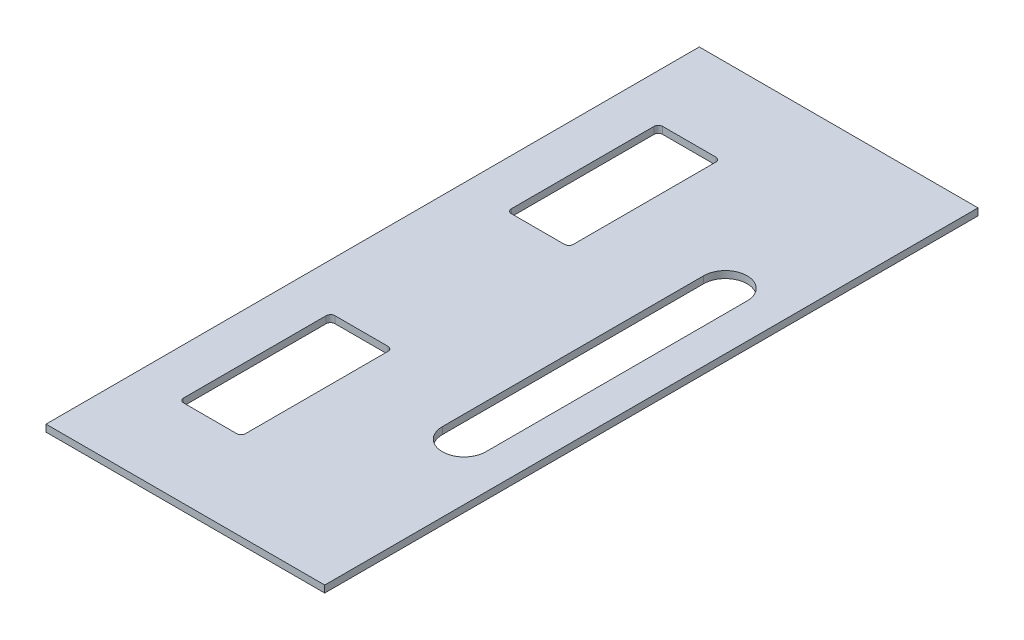
SolidWorks part; units mm, degrees
ref_plane "Front Plane" through (0, 0, 0) normal (0, 0, 1) x (1, 0, 0)
ref_plane "Top Plane" through (0, 0, 0) normal (0, 1, 0) x (1, 0, 0)
ref_plane "Right Plane" through (0, 0, 0) normal (1, 0, 0) x (0, 0, -1)
sketch "Sketch4" plane through (0, 0, 0) normal (0, 1, 0) x (1, 0, 0)
  line L0 (0, 0) -> (320, 0)
  line L2 (0, 750) -> (320, 750)
  line L3 (0, 750) -> (0, 0)
  line L4 (0, 0) -> (320, 0)
  line L5 (320, 750) -> (320, 0)
  dimension "D1" = 320
  dimension "D2" = 750
extrude "Boss-Extrude3" add sketch "Sketch4" along normal blind 8 contours L5 L2 L3 L0
sketch "Sketch8" plane through (0, 8, 0) normal (0, 1, 0) x (1, 0, 0)
  line L0 (-4.4, 0) -> (4.4, 0) construction
  line L1 (119, 100) -> (58, 100)
  line L2 (124, 105) -> (124, 268.6758)
  line L3 (119, 273.6758) -> (58, 273.6758)
  line L4 (53, 105) -> (53, 268.6758)
  line L5 (0, 750) -> (0, 0) construction
  line L6 (0, 375) -> (320, 375) construction
  line L7 (320, 750) -> (320, 0) construction
  line L8 (255, 225) -> (255, 525) construction
  line L9 (230, 225) -> (230, 525)
  line L10 (280, 225) -> (280, 525)
  line L11 (119, 476.3242) -> (58, 476.3242)
  line L12 (53, 645) -> (53, 481.3242)
  line L13 (119, 650) -> (58, 650)
  line L14 (124, 645) -> (124, 481.3242)
  arc A0 (230, 225) -> (280, 225) centre (255, 225) ccw
  arc A1 (280, 525) -> (230, 525) centre (255, 525) ccw
  arc A2 (58, 100) -> (53, 105) centre (58, 105) cw
  arc A3 (119, 100) -> (124, 105) centre (119, 105) ccw
  arc A4 (124, 268.6758) -> (119, 273.6758) centre (119, 268.6758) ccw
  arc A5 (58, 273.6758) -> (53, 268.6758) centre (58, 268.6758) ccw
  arc A6 (58, 476.3242) -> (53, 481.3242) centre (58, 481.3242) cw
  arc A7 (58, 650) -> (53, 645) centre (58, 645) ccw
  arc A8 (119, 650) -> (124, 645) centre (119, 645) cw
  arc A9 (124, 481.3242) -> (119, 476.3242) centre (119, 481.3242) cw
  point P10 (255, 375)
  point P21 (53, 100)
  point P24 (124, 100)
  dimension "D7" = 5
  dimension "D1" = 100
  dimension "D2" = 53
  dimension "D3" = 71
  dimension "D4" = 0
  dimension "D5" = 150
  dimension "D6" = 25
  dimension "D8" = 65
extrude "Cut-Extrude1" cut sketch "Sketch8" against normal blind 8 contours L11 A6 L12 A7 L13 A8 L14 A9 | L10 A1 L9 A0 | L2 A4 L3 A5 L4 A2 L1 A3
